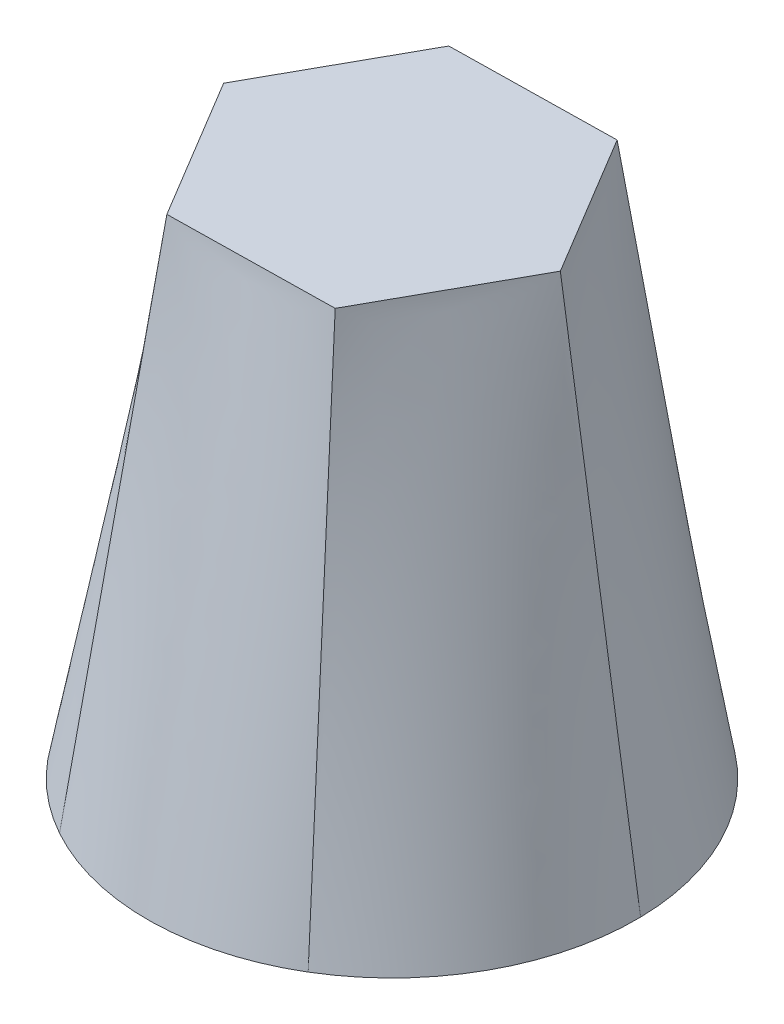
SolidWorks part; units mm, degrees
ref_plane "Front Plane" through (0, 0, 0) normal (0, 0, 1) x (1, 0, 0)
ref_plane "Top Plane" through (0, 0, 0) normal (0, 1, 0) x (1, 0, 0)
ref_plane "Right Plane" through (0, 0, 0) normal (1, 0, 0) x (0, 0, -1)
sketch "Sketch1" plane through (0, 0, 0) normal (0, 1, 0) x (1, 0, 0)
  circle A0 centre (0, 0) radius 65.7401
ref_plane "Plane1" through (0, 140, 0) normal (0, 1, 0) x (1, 0, 0)
sketch "Sketch2" plane through (0, 140, 0) normal (0, 1, 0) x (1, 0, 0)
  line L1 (22.9069, -38.1781) -> (44.5166, 0.7489)
  line L2 (44.5166, 0.7489) -> (21.6098, 38.927)
  line L3 (21.6098, 38.927) -> (-22.9069, 38.1781)
  line L4 (-22.9069, 38.1781) -> (-44.5166, -0.7489)
  line L5 (-44.5166, -0.7489) -> (-21.6098, -38.927)
  line L6 (-21.6098, -38.927) -> (22.9069, -38.1781)
  circle A0 centre (0, 0) radius 38.558 construction
loft "Loft2" add profiles "Sketch2", "Sketch1"
